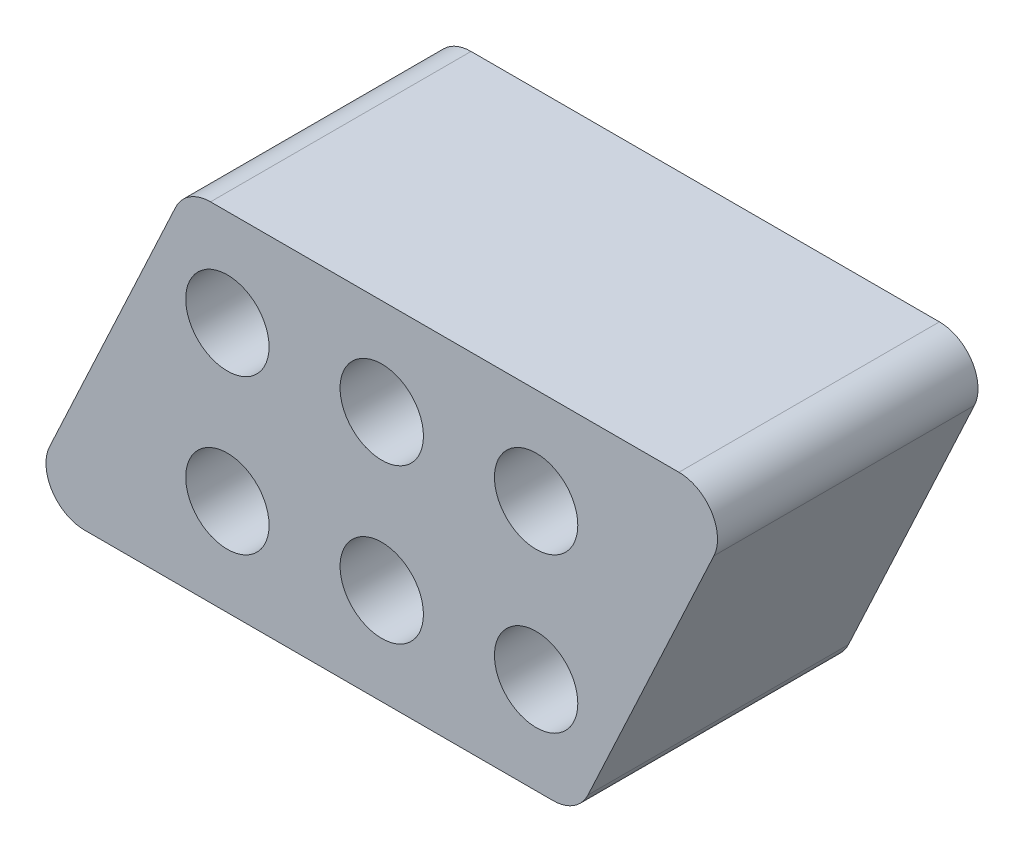
SolidWorks part; units mm, degrees
ref_plane "Front Plane" through (0, 0, 0) normal (0, 0, 1) x (1, 0, 0)
ref_plane "Top Plane" through (0, 0, 0) normal (0, 1, 0) x (1, 0, 0)
ref_plane "Right Plane" through (0, 0, 0) normal (1, 0, 0) x (0, 0, -1)
sketch "Sketch1" plane through (0, 0, 0) normal (0, 0, 1) x (1, 0, 0)
  line L0 (-24.4496, -14.2875) -> (14.0859, -14.2875)
  line L1 (16.9634, -12.4543) -> (27.3271, 9.7707)
  line L2 (24.4496, 14.2875) -> (-14.0859, 14.2875)
  line L3 (-16.9634, 12.4543) -> (-27.3271, -9.7707)
  line L4 (0, 6.35) -> (0, -6.35) construction
  line L5 (-29.4333, -14.2875) -> (29.4333, 14.2875) construction
  circle A0 centre (-12.7, -6.35) radius 3.429
  circle A1 centre (0, -6.35) radius 3.429
  circle A2 centre (12.7, -6.35) radius 3.429
  circle A3 centre (0, 6.35) radius 3.429
  circle A4 centre (12.7, 6.35) radius 3.429
  circle A5 centre (-12.7, 6.35) radius 3.429
  arc A6 (-24.4496, -14.2875) -> (-27.3271, -9.7707) centre (-24.4496, -11.1125) cw
  arc A7 (14.0859, -14.2875) -> (16.9634, -12.4543) centre (14.0859, -11.1125) ccw
  arc A8 (27.3271, 9.7707) -> (24.4496, 14.2875) centre (24.4496, 11.1125) ccw
  arc A9 (-14.0859, 14.2875) -> (-16.9634, 12.4543) centre (-14.0859, 11.1125) ccw
  point P6 (0, 0)
  point P7 (0, 0)
  dimension "D4" = 6.858
  dimension "D7" = 12.7
  dimension "D8" = 12.7
  dimension "D9" = 3.175
  dimension "D1" = 65
  dimension "D2" = 41.275
  dimension "D3" = 28.575
  dimension "D5" = 3
  dimension "D6" = 2
extrude "Boss-Extrude1" add sketch "Sketch1" along normal blind 21.4312
